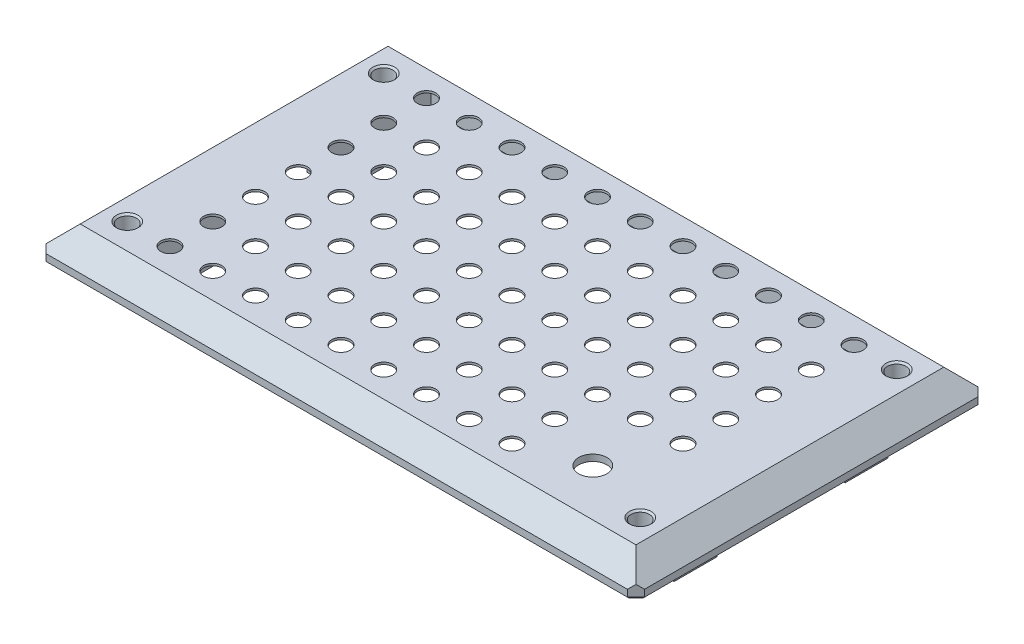
SolidWorks part; units mm, degrees
ref_plane "Front Plane" through (0, 0, 0) normal (0, 0, 1) x (1, 0, 0)
ref_plane "Top Plane" through (0, 0, 0) normal (0, 1, 0) x (1, 0, 0)
ref_plane "Right Plane" through (0, 0, 0) normal (1, 0, 0) x (0, 0, -1)
sketch "Sketch1" plane through (0, 0, 0) normal (0, 1, 0) x (1, 0, 0)
  line L1 (-70, -41) -> (70, -41)
  line L2 (-70, -41) -> (-70, 41)
  line L3 (-70, 41) -> (70, 41)
  line L4 (70, -41) -> (70, 41)
  line L5 (-70, -41) -> (70, 41) construction
  line L6 (-70, 41) -> (70, -41) construction
  point P0 (0, 0)
  dimension "D1" = 140
  dimension "D2" = 82
extrude "Boss-Extrude1" add sketch "Sketch1" along normal blind 2
sketch "Sketch2" plane through (0, 2, 0) normal (0, 1, 0) x (1, 0, 0)
  line L4 (70, -41) -> (70, 41)
  line L5 (70, 41) -> (-70, 41)
  line L6 (-70, 41) -> (-70, -41)
  line L7 (-70, -41) -> (70, -41)
  line L8 (70, -41) -> (70, 41)
  line L9 (70, 41) -> (-70, 41)
  line L10 (-70, 41) -> (-70, -41)
  line L11 (-70, -41) -> (70, -41)
  dimension "D1" = 0
ref_plane "Plane1" through (0, 7, 0) normal (0, 1, 0) x (1, 0, 0)
sketch "Sketch3" plane through (0, 7, 0) normal (0, 1, 0) x (1, 0, 0)
  line L0 (-70, 41) -> (-70, -41) construction
  line L1 (-65, -36) -> (65, -36)
  line L2 (-65, -36) -> (-65, 36)
  line L3 (-65, 36) -> (65, 36)
  line L4 (65, -36) -> (65, 36)
  line L5 (-65, -36) -> (65, 36) construction
  line L6 (-65, 36) -> (65, -36) construction
  line L7 (70, 41) -> (-70, 41) construction
  point P0 (0, 0)
  dimension "D1" = 5
  dimension "D2" = 5
loft "Loft1" add profiles "Sketch3", "Sketch2"
chamfer "Chamfer2" distance 2 angle 45 4 edges at (70, 1, 41) (70, 1, -41) (-70, 1, -41) (-70, 1, 41)
sketch "Sketch4" plane through (0, 0, 0) normal (0, -1, 0) x (1, 0, 0)
  line L0 (-70, -39) -> (-70, 39) construction
  line L1 (-62.9, 15) -> (-54.9, 15)
  line L2 (-62.9, 15) -> (-62.9, 25)
  line L3 (-62.9, 25) -> (-54.9, 25)
  line L4 (-54.9, 15) -> (-54.9, 25)
  line L5 (-62.9, 15) -> (-54.9, 25) construction
  line L6 (-62.9, 25) -> (-54.9, 15) construction
  line L7 (-70, 0) -> (70, 0) construction
  line L8 (70, 39) -> (70, -39) construction
  line L9 (0, 41) -> (0, -41) construction
  line L10 (-68, 41) -> (68, 41) construction
  line L11 (68, -41) -> (-68, -41) construction
  line L12 (-62.9, -25) -> (-54.9, -15) construction
  line L13 (-62.9, -15) -> (-54.9, -25) construction
  line L14 (-54.9, -15) -> (-54.9, -25)
  line L15 (-62.9, -25) -> (-54.9, -25)
  line L16 (-62.9, -15) -> (-62.9, -25)
  line L17 (-62.9, -15) -> (-54.9, -15)
  line L18 (62.9, -15) -> (54.9, -25) construction
  line L19 (62.9, -25) -> (54.9, -15) construction
  line L20 (62.9, 25) -> (54.9, 15) construction
  line L21 (62.9, 15) -> (54.9, 25) construction
  line L22 (62.9, -15) -> (54.9, -15)
  line L23 (62.9, -15) -> (62.9, -25)
  line L24 (62.9, -25) -> (54.9, -25)
  line L25 (54.9, -15) -> (54.9, -25)
  line L26 (54.9, 15) -> (54.9, 25)
  line L27 (62.9, 25) -> (54.9, 25)
  line L28 (62.9, 15) -> (62.9, 25)
  line L29 (62.9, 15) -> (54.9, 15)
  point P0 (-58.9, 20)
  point P21 (-58.9, -20)
  point P30 (58.9, -20)
  point P31 (58.9, 20)
  dimension "D1" = 10
  dimension "D2" = 7.1
  dimension "D3" = 8
  dimension "D4" = 40
extrude "Boss-Extrude2" add sketch "Sketch4" along normal blind 7
sketch "Sketch5" plane through (-62.9, 0, 0) normal (-1, 0, 0) x (0, 0, 1)
  line L0 (-15, 0) -> (-25, -7) construction
  line L1 (0, 0) -> (0, 50000) construction
  circle A0 centre (-20, -3.5) radius 2.05
  circle A1 centre (20, -3.5) radius 2.05
  dimension "D1" = 4.1
extrude "Cut-Extrude1" cut sketch "Sketch5" against normal through all
sketch "Sketch6" plane through (0, 0, 0) normal (0, -1, 0) x (1, 0, 0)
  line L0 (54.9, 25) -> (54.9, 15) construction
  line L1 (-53.9, -35) -> (53.9, -35)
  line L2 (-53.9, -35) -> (-53.9, 35)
  line L3 (-53.9, 35) -> (53.9, 35)
  line L4 (53.9, -35) -> (53.9, 35)
  line L5 (-53.9, -35) -> (53.9, 35) construction
  line L6 (-53.9, 35) -> (53.9, -35) construction
  line L8 (-65, 36) -> (65, 36) construction
  point P0 (0, 0)
  dimension "D1" = 1
  dimension "D2" = 1
extrude "Cut-Extrude2" cut sketch "Sketch6" against normal offset from surface (5.5 mm away) 1.5 up to face at (0, 7, 0)
sketch "Sketch7" plane through (0, 5.5, 0) normal (0, -1, 0) x (1, 0, 0)
  line L0 (0, 35) -> (0, -35) construction
  line L1 (-53.9, 35) -> (53.9, 35) construction
  line L2 (-53.9, -35) -> (53.9, -35) construction
  line L3 (-53.9, 0) -> (53.9, 0) construction
  line L4 (-53.9, -35) -> (-53.9, 35) construction
  line L5 (53.9, 35) -> (53.9, -35) construction
  circle A0 centre (0, 0) radius 2.15
  circle A1 centre (10, 0) radius 2.15
  circle A2 centre (20, 0) radius 2.15
  circle A3 centre (30, 0) radius 2.15
  circle A4 centre (40, 0) radius 2.15
  circle A5 centre (50, 0) radius 2.15
  circle A7 centre (10, 10) radius 2.15
  circle A8 centre (20, 10) radius 2.15
  circle A9 centre (30, 10) radius 2.15
  circle A10 centre (40, 10) radius 2.15
  circle A11 centre (50, 10) radius 2.15
  circle A13 centre (10, 20) radius 2.15
  circle A14 centre (20, 20) radius 2.15
  circle A15 centre (30, 20) radius 2.15
  circle A16 centre (40, 20) radius 2.15
  circle A17 centre (50, 20) radius 2.15
  circle A19 centre (10, 30) radius 2.15
  circle A20 centre (20, 30) radius 2.15
  circle A21 centre (30, 30) radius 2.15
  circle A22 centre (40, 30) radius 2.15
  circle A23 centre (50, 30) radius 2.15
  circle A25 centre (0, 10) radius 2.15
  circle A26 centre (0, 20) radius 2.15
  circle A27 centre (0, 30) radius 2.15
  circle A35 centre (-50, 30) radius 2.15
  circle A36 centre (-40, 30) radius 2.15
  circle A37 centre (-30, 30) radius 2.15
  circle A38 centre (-20, 30) radius 2.15
  circle A39 centre (-10, 30) radius 2.15
  circle A40 centre (-50, 20) radius 2.15
  circle A41 centre (-40, 20) radius 2.15
  circle A42 centre (-30, 20) radius 2.15
  circle A43 centre (-20, 20) radius 2.15
  circle A44 centre (-10, 20) radius 2.15
  circle A45 centre (-50, 10) radius 2.15
  circle A46 centre (-40, 10) radius 2.15
  circle A47 centre (-30, 10) radius 2.15
  circle A48 centre (-20, 10) radius 2.15
  circle A49 centre (-10, 10) radius 2.15
  circle A50 centre (-50, 0) radius 2.15
  circle A51 centre (-40, 0) radius 2.15
  circle A52 centre (-30, 0) radius 2.15
  circle A53 centre (-20, 0) radius 2.15
  circle A54 centre (-10, 0) radius 2.15
  circle A55 centre (-10, -10) radius 2.15
  circle A56 centre (-20, -10) radius 2.15
  circle A57 centre (-30, -10) radius 2.15
  circle A58 centre (-40, -10) radius 2.15
  circle A59 centre (-50, -10) radius 2.15
  circle A60 centre (-10, -20) radius 2.15
  circle A61 centre (-20, -20) radius 2.15
  circle A62 centre (-30, -20) radius 2.15
  circle A63 centre (-40, -20) radius 2.15
  circle A64 centre (-50, -20) radius 2.15
  circle A65 centre (-10, -30) radius 2.15
  circle A66 centre (-20, -30) radius 2.15
  circle A67 centre (-30, -30) radius 2.15
  circle A68 centre (-40, -30) radius 2.15
  circle A69 centre (-50, -30) radius 2.15
  circle A70 centre (0, -30) radius 2.15
  circle A71 centre (0, -20) radius 2.15
  circle A72 centre (0, -10) radius 2.15
  circle A73 centre (50, -30) radius 2.15
  circle A74 centre (40, -30) radius 2.15
  circle A75 centre (30, -30) radius 2.15
  circle A76 centre (20, -30) radius 2.15
  circle A77 centre (10, -30) radius 2.15
  circle A78 centre (50, -20) radius 2.15
  circle A79 centre (40, -20) radius 2.15
  circle A80 centre (30, -20) radius 2.15
  circle A81 centre (20, -20) radius 2.15
  circle A82 centre (10, -20) radius 2.15
  circle A83 centre (50, -10) radius 2.15
  circle A84 centre (40, -10) radius 2.15
  circle A85 centre (30, -10) radius 2.15
  circle A86 centre (20, -10) radius 2.15
  circle A87 centre (10, -10) radius 2.15
  dimension "D1" = 4.3
  dimension "D2" = 6
  dimension "D3" = 4
extrude "Cut-Extrude3" cut sketch "Sketch7" against normal through all
sketch "Sketch8" plane through (0, 5.5, 0) normal (0, -1, 0) x (1, 0, 0)
  line L0 (0, 35) -> (0, -35) construction
  line L1 (-53.9, 35) -> (53.9, 35) construction
  line L2 (53.9, -35) -> (-53.9, -35) construction
  line L3 (-53.9, 0) -> (53.9, 0) construction
  line L4 (-53.9, -35) -> (-53.9, 35) construction
  line L5 (53.9, -35) -> (53.9, 35) construction
  circle A0 centre (0, 0) radius 4.2
  circle A1 centre (10, 0) radius 4.2
  circle A2 centre (20, 0) radius 4.2
  circle A3 centre (30, 0) radius 4.2
  circle A4 centre (40, 0) radius 4.2
  circle A5 centre (50, 0) radius 4.2
  circle A6 centre (10, 10) radius 4.2
  circle A7 centre (20, 10) radius 4.2
  circle A8 centre (30, 10) radius 4.2
  circle A9 centre (40, 10) radius 4.2
  circle A10 centre (50, 10) radius 4.2
  circle A11 centre (10, 20) radius 4.2
  circle A12 centre (20, 20) radius 4.2
  circle A13 centre (30, 20) radius 4.2
  circle A14 centre (40, 20) radius 4.2
  circle A15 centre (50, 20) radius 4.2
  circle A16 centre (10, 30) radius 4.2
  circle A17 centre (20, 30) radius 4.2
  circle A18 centre (30, 30) radius 4.2
  circle A19 centre (40, 30) radius 4.2
  circle A20 centre (50, 30) radius 4.2
  circle A21 centre (0, 10) radius 4.2
  circle A22 centre (0, 20) radius 4.2
  circle A23 centre (0, 30) radius 4.2
  circle A24 centre (0, -30) radius 4.2
  circle A25 centre (0, -20) radius 4.2
  circle A26 centre (0, -10) radius 4.2
  circle A27 centre (50, -30) radius 4.2
  circle A28 centre (40, -30) radius 4.2
  circle A29 centre (30, -30) radius 4.2
  circle A30 centre (20, -30) radius 4.2
  circle A31 centre (10, -30) radius 4.2
  circle A32 centre (50, -20) radius 4.2
  circle A33 centre (40, -20) radius 4.2
  circle A34 centre (30, -20) radius 4.2
  circle A35 centre (20, -20) radius 4.2
  circle A36 centre (10, -20) radius 4.2
  circle A37 centre (50, -10) radius 4.2
  circle A38 centre (40, -10) radius 4.2
  circle A39 centre (30, -10) radius 4.2
  circle A40 centre (20, -10) radius 4.2
  circle A41 centre (10, -10) radius 4.2
  circle A42 centre (-10, -10) radius 4.2
  circle A43 centre (-20, -10) radius 4.2
  circle A44 centre (-30, -10) radius 4.2
  circle A45 centre (-40, -10) radius 4.2
  circle A46 centre (-50, -10) radius 4.2
  circle A47 centre (-10, -20) radius 4.2
  circle A48 centre (-20, -20) radius 4.2
  circle A49 centre (-30, -20) radius 4.2
  circle A50 centre (-40, -20) radius 4.2
  circle A51 centre (-50, -20) radius 4.2
  circle A52 centre (-10, -30) radius 4.2
  circle A53 centre (-20, -30) radius 4.2
  circle A54 centre (-30, -30) radius 4.2
  circle A55 centre (-40, -30) radius 4.2
  circle A56 centre (-50, -30) radius 4.2
  circle A57 centre (-50, 30) radius 4.2
  circle A58 centre (-40, 30) radius 4.2
  circle A59 centre (-30, 30) radius 4.2
  circle A60 centre (-20, 30) radius 4.2
  circle A61 centre (-10, 30) radius 4.2
  circle A62 centre (-50, 20) radius 4.2
  circle A63 centre (-40, 20) radius 4.2
  circle A64 centre (-30, 20) radius 4.2
  circle A65 centre (-20, 20) radius 4.2
  circle A66 centre (-10, 20) radius 4.2
  circle A67 centre (-50, 10) radius 4.2
  circle A68 centre (-40, 10) radius 4.2
  circle A69 centre (-30, 10) radius 4.2
  circle A70 centre (-20, 10) radius 4.2
  circle A71 centre (-10, 10) radius 4.2
  circle A72 centre (-50, 0) radius 4.2
  circle A73 centre (-40, 0) radius 4.2
  circle A74 centre (-30, 0) radius 4.2
  circle A75 centre (-20, 0) radius 4.2
  circle A76 centre (-10, 0) radius 4.2
  dimension "D1" = 8.4
  dimension "D2" = 6
  dimension "D3" = 4
extrude "Cut-Extrude4" cut sketch "Sketch8" against normal blind 1
sketch "Sketch9" plane through (0, 7, 0) normal (0, 1, 0) x (1, 0, 0)
  line L1 (53.9, -35) -> (34.6, -35)
  line L2 (53.9, -35) -> (53.9, -15.5)
  line L3 (53.9, -15.5) -> (34.6, -15.5)
  line L4 (34.6, -35) -> (34.6, -15.5)
  dimension "D1" = 19.3
  dimension "D2" = 19.5
sketch "Sketch13" plane through (0, 5.5, 0) normal (0, -1, 0) x (1, 0, 0)
  circle A0 centre (50, 20) radius 4.2 construction
  circle A1 centre (40, 20) radius 4.2 construction
  circle A2 centre (40, 30) radius 4.2 construction
  circle A3 centre (50, 30) radius 4.2 construction
  circle A4 centre (50, 20) radius 4.2
  circle A5 centre (40, 20) radius 4.2
  circle A6 centre (40, 30) radius 4.2
  circle A7 centre (50, 30) radius 4.2
extrude "Boss-Extrude4" add sketch "Sketch13" against normal up to surface (1.5 mm away) up to face at (-30, 7, -2.15)
sketch "Sketch10" plane through (0, 5.5, 0) normal (0, -1, 0) x (1, 0, 0)
  line L1 (53.9, 35) -> (43.9, 35) construction
  line L2 (53.9, 35) -> (53.9, 25) construction
  line L3 (53.9, 25) -> (43.9, 25) construction
  line L4 (43.9, 35) -> (43.9, 25) construction
  circle A0 centre (43.9, 25) radius 3.3
  dimension "D1" = 6.6
  dimension "D2" = 10
extrude "Cut-Extrude5" cut sketch "Sketch10" against normal through all
sketch "Sketch11" plane through (0, 0, 0) normal (0, -1, 0) x (1, 0, 0)
  line L0 (53.9, 35) -> (53.9, 11.5588) construction
  line L1 (53.9, 10) -> (63.9, 10)
  line L2 (53.9, 10) -> (53.9, -10)
  line L3 (53.9, -10) -> (63.9, -10)
  line L4 (63.9, 10) -> (63.9, -10)
  line L5 (-53.9, 35) -> (-53.9, -35) construction
  line L6 (-53.9, 10) -> (-63.9, 10)
  line L7 (-53.9, 10) -> (-53.9, -10)
  line L8 (-53.9, -10) -> (-63.9, -10)
  line L9 (-63.9, 10) -> (-63.9, -10)
  line L10 (-70, -39) -> (-70, 39) construction
  point P12 (-63.9, 0)
  point P15 (-70, 0)
  point P16 (63.9, 0)
  dimension "D1" = 10
  dimension "D2" = 20
extrude "Cut-Extrude6" cut sketch "Sketch11" against normal up to surface (5.5 mm away) up to face at (43.9, 5.5, 21.7)
sketch "Sketch12" plane through (0, 0, 0) normal (0, -1, 0) x (1, 0, 0)
  line L0 (0, 0) -> (-60, 0) construction
  line L1 (-60, -30) -> (-60, 30) construction
  line L2 (-70, -39) -> (-70, 39) construction
  line L3 (0, 41) -> (0, -41) construction
  line L4 (-68, 41) -> (68, 41) construction
  line L5 (68, -41) -> (-68, -41) construction
  line L6 (60, -30) -> (60, 30) construction
  circle A0 centre (-60, 30) radius 2.15
  circle A1 centre (-60, -30) radius 2.15
  circle A2 centre (60, -30) radius 2.15
  circle A3 centre (60, 30) radius 2.15
  point P6 (-60, 0)
  point P20 (60, 0)
  dimension "D1" = 4.3
  dimension "D2" = 60
  dimension "D3" = 10
extrude "Cut-Extrude7" cut sketch "Sketch12" against normal through all
chamfer "Chamfer3" distance 0.4 angle 45 8 edges at (-69, 0, -40) (-70, 0, 0) (-69, 0, 40) (0, 0, 41) (69, 0, 40) (70, 0, 0) (69, 0, -40) (0, 0, -41)
chamfer "Chamfer4" distance 0.4 angle 45 4 edges at (60, 7, 27.85) (60, 7, -32.15) (-60, 7, 27.85) (-60, 7, -32.15)
chamfer "Chamfer5" distance 0.4 angle 45 4 edges at (-62.9, -3.5, 17.95) (-62.9, -3.5, -17.95) (62.9, -3.5, 22.05) (62.9, -3.5, -17.95)
